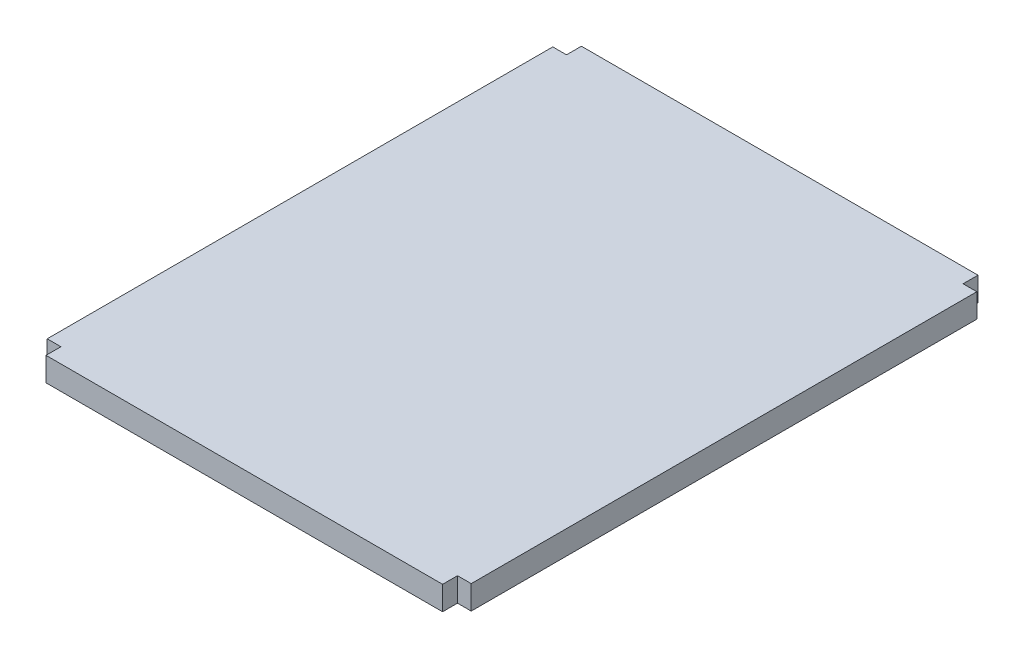
SolidWorks part; units mm, degrees
material "Polyurethane Foam Flexible"
ref_plane "Front Plane" through (0, 0, 0) normal (0, 0, 1) x (1, 0, 0)
ref_plane "Top Plane" through (0, 0, 0) normal (0, 1, 0) x (1, 0, 0)
ref_plane "Right Plane" through (0, 0, 0) normal (1, 0, 0) x (0, 0, -1)
sketch "Sketch1" plane through (0, 0, 0) normal (0, 1, 0) x (1, 0, 0)
  line L1 (-1057.148, -1427.226) -> (1057.148, -1427.226)
  line L2 (-1130.3, -1347.724) -> (-1130.3, 1347.724)
  line L3 (-1057.148, 1427.226) -> (1057.148, 1427.226)
  line L4 (1130.3, -1347.724) -> (1130.3, 1347.724)
  line L5 (-1067.3379, -1347.724) -> (1067.3379, 1347.724) construction
  line L11 (-1057.148, 1347.724) -> (-1130.3, 1347.724)
  line L12 (-1057.148, 1347.724) -> (-1057.148, 1427.226)
  line L17 (1130.3, 1347.724) -> (1057.148, 1347.724)
  line L18 (1057.148, 1347.724) -> (1057.148, 1427.226)
  line L22 (1057.148, -1427.226) -> (1057.148, -1347.724)
  line L23 (1130.3, -1347.724) -> (1057.148, -1347.724)
  line L24 (-1057.148, -1427.226) -> (-1057.148, -1347.724)
  line L27 (-1057.148, -1347.724) -> (-1130.3, -1347.724)
  line L28 (-1067.3379, 1347.724) -> (1067.3379, -1347.724) construction
  line L29 (1130.3, 1347.724) -> (1130.3, 1427.226) [skipped]
  line L30 (1130.3, -1427.226) -> (1057.148, -1427.226) [skipped]
  line L31 (1130.3, -1427.226) -> (1130.3, -1347.724) [skipped]
  line L32 (-1057.148, -1427.226) -> (-1130.3, -1427.226) [skipped]
  point P0 (0, 0)
  point P2 (0, 0)
  point P6 (0, 0)
  point P7 (0, 0)
  point P11 (0, 0)
  point P13 (0, 1427.226)
  point P16 (1130.3, 0)
  point P19 (1057.148, 1427.226)
  point P25 (1057.148, 1347.724)
  point P34 (1067.3379, 1347.724)
  point P35 (1130.3, 1347.724)
  point P36 (1057.148, -1427.226)
  point P37 (0, 0)
  point P38 (0, 0)
  dimension "D1" = 2854.452
  dimension "D2" = 2260.6
  dimension "D3" = 73.152
  dimension "D4" = 79.502
  dimension "D5" = 2
  dimension "D6" = 2
extrude "Boss-Extrude1" add sketch "Sketch1" along normal blind 127
